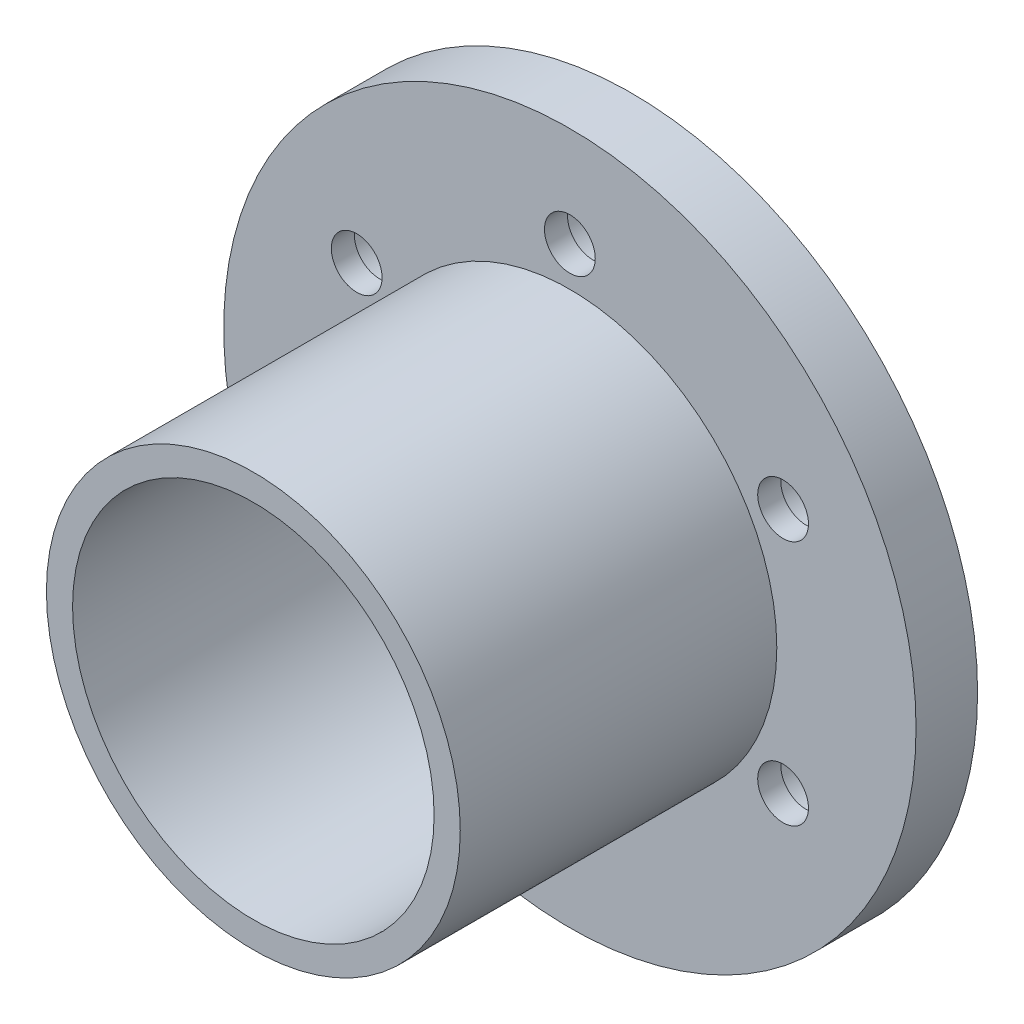
SolidWorks part; units mm, degrees
material "Stainless Steel (ferritic)"
ref_plane "Front Plane" through (0, 0, 0) normal (0, 0, 1) x (1, 0, 0)
ref_plane "Top Plane" through (0, 0, 0) normal (0, 1, 0) x (1, 0, 0)
ref_plane "Right Plane" through (0, 0, 0) normal (1, 0, 0) x (0, 0, -1)
sketch "Sketch2" plane through (0, 0, 0) normal (0, 0, 1) x (1, 0, 0)
  circle A0 centre (0, 0) radius 45
  dimension "D1" = 90
extrude "Boss-Extrude1" add sketch "Sketch2" along normal blind 8
sketch "Sketch5" plane through (0, 0, 8) normal (0, 0, 1) x (1, 0, 0)
  circle A0 centre (0, 0) radius 23.5
  dimension "D1" = 47
extrude "Cut-Extrude1" cut sketch "Sketch5" against normal through all
sketch "Sketch6" plane through (0, 0, 8) normal (0, 0, 1) x (1, 0, 0)
  circle A1 centre (0, 0) radius 26.9
  dimension "D1" = 53.8
extrude "Boss-Extrude2" add sketch "Sketch6" along normal blind 41.148
sketch "Sketch7" plane through (0, 0, 49.148) normal (0, 0, 1) x (1, 0, 0)
  circle A0 centre (0, 0) radius 23.5
  dimension "D1" = 47
extrude "Cut-Extrude3" cut sketch "Sketch7" against normal through all
sketch "Sketch8" plane through (0, 0, 0) normal (0, 0, -1) x (-1, 0, 0)
  line L0 (0, 0) -> (0, 32) construction
  dimension "D1" = 32
hole_wizard "CBORE for M8 Hex Head Bolt1" positions "3DSketch1" profile "Sketch9" counterbore size "M8" standard "ANSI Metric" end condition through all
sketch3d "3DSketch1"
  point P0 (0, 32, 0)
sketch "Sketch9" plane through (0, 32, 0) normal (1, 0, 0) x (0, 1, 0)
  line L0 (0, 0) -> (0, 49.148)
  line L1 (0, 49.148) -> (3.3, 49.148)
  line L3 (3.3, 49.148) -> (3.3, 5)
  line L4 (3.3, 5) -> (5, 5)
  line L5 (5, 5) -> (5, 0)
  line L7 (5, 0) -> (0, 0)
  line L11 (0, -6.35) -> (0, 107.95) construction
  dimension "Thru Hole Dia." = 6.6
  dimension "Thru Hole Depth" = 49.148
  dimension "C'Bore Dia." = 10
  dimension "C'Bore Depth" = 5
pattern_circular "CirPattern1" count 6 over 360 about axis through (0, 0, 0) along (0, 0, 1) of "CBORE for M8 Hex Head Bolt1"
